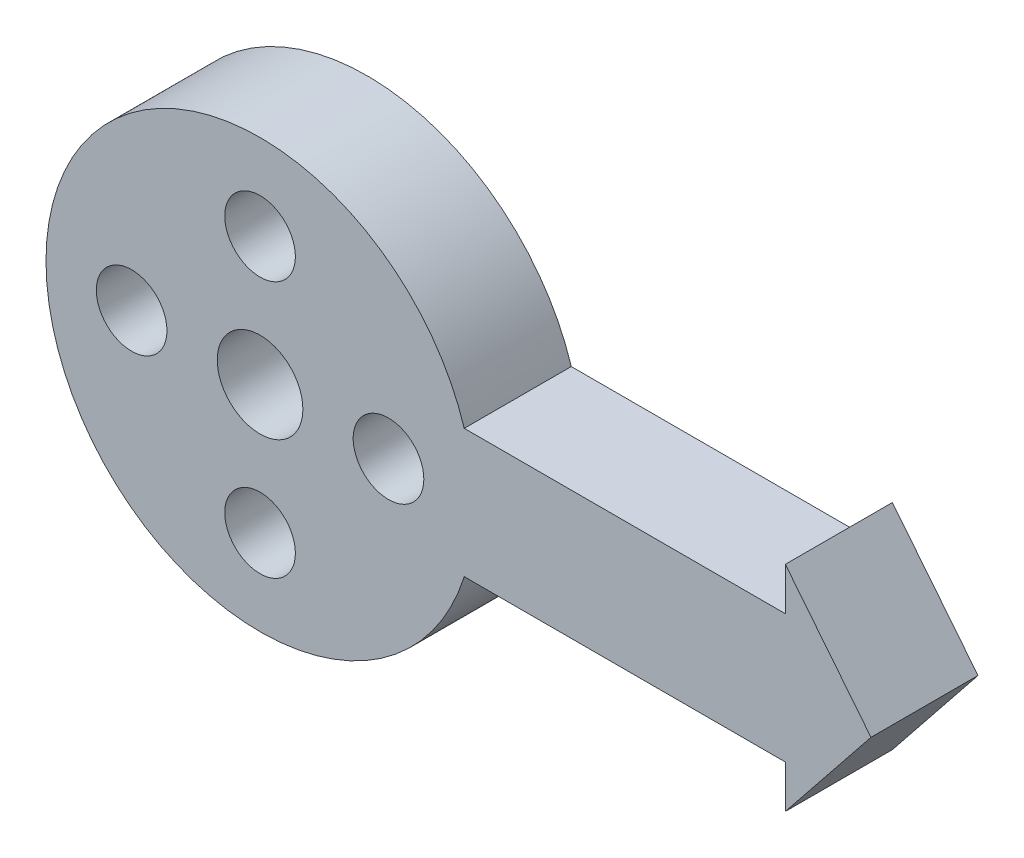
SolidWorks part; units mm, degrees
ref_plane "Front Plane" through (0, 0, 0) normal (0, 0, 1) x (1, 0, 0)
ref_plane "Top Plane" through (0, 0, 0) normal (0, 1, 0) x (1, 0, 0)
ref_plane "Right Plane" through (0, 0, 0) normal (1, 0, 0) x (0, 0, -1)
sketch "Sketch1" plane through (0, 0, 0) normal (0, 0, 1) x (1, 0, 0)
  line L0 (9.5394, 3) -> (24.5394, 3)
  line L1 (24.5394, 3) -> (24.5394, 5)
  line L2 (24.5394, 5) -> (28.5394, 0)
  line L3 (28.5394, 0) -> (24.5394, -5)
  line L4 (24.5394, -5) -> (24.5394, -3)
  line L5 (24.5394, -3) -> (9.5394, -3)
  arc A0 (9.5394, 3) -> (9.5394, -3) centre (0, 0) ccw
  circle A1 centre (0, 0) radius 2
  circle A2 centre (0, 6) radius 1.65
  circle A3 centre (6, 0) radius 1.65
  circle A4 centre (0, -6) radius 1.65
  circle A5 centre (-6, 0) radius 1.65
  point P15 (0, 0)
  dimension "D1" = 20
  dimension "D2" = 4
  dimension "D4" = 3.3
  dimension "D3" = 6
  dimension "D6" = 6
  dimension "D7" = 3
  dimension "D8" = 2
  dimension "D9" = 4
  dimension "D10" = 15
  dimension "D5" = 4
extrude "Boss-Extrude1" add sketch "Sketch1" along normal blind 5
